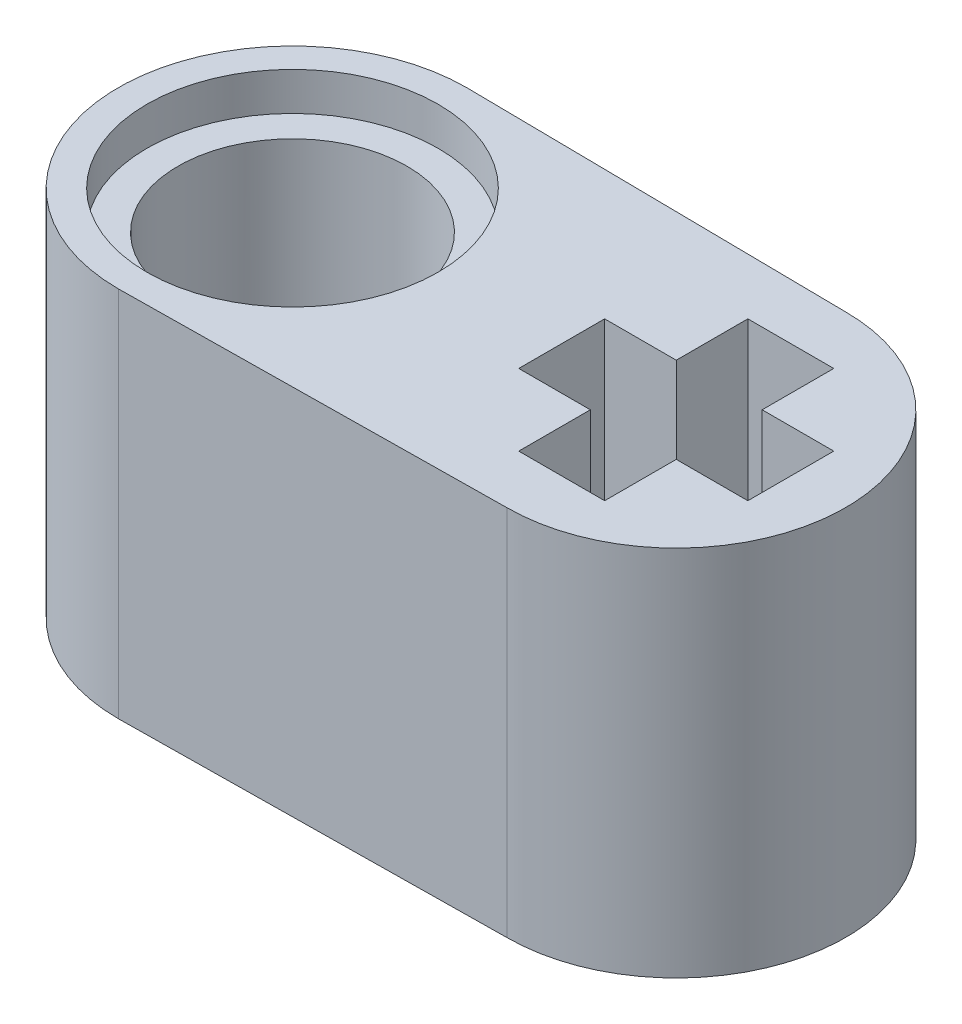
SolidWorks part; units mm, degrees
ref_plane "Front Plane" through (0, 0, 0) normal (0, 0, 1) x (1, 0, 0)
ref_plane "Top Plane" through (0, 0, 0) normal (0, 1, 0) x (1, 0, 0)
ref_plane "Right Plane" through (0, 0, 0) normal (1, 0, 0) x (0, 0, -1)
sketch "Sketch1" plane through (0, 0, 0) normal (0, 1, 0) x (1, 0, 0)
  line L0 (-1.67, 0) -> (3.97, 0) construction
  line L1 (-55, 0) -> (55, 0) construction
  line L2 (-4.07, 3.65) -> (3.97, 3.55)
  line L3 (-4.07, -3.65) -> (3.97, -3.55)
  line L6 (3.07, 2.4) -> (3.07, 0.9)
  line L7 (3.07, 2.4) -> (4.87, 2.4)
  line L8 (3.07, -2.4) -> (4.87, -2.4)
  line L9 (4.87, 2.4) -> (4.87, 0.9)
  line L10 (3.07, 2.4) -> (4.87, -2.4) construction
  line L11 (3.07, -2.4) -> (4.87, 2.4) construction
  line L12 (6.37, -0.9) -> (4.87, -0.9)
  line L13 (6.37, -0.9) -> (6.37, 0.9)
  line L14 (1.57, -0.9) -> (1.57, 0.9)
  line L15 (6.37, 0.9) -> (4.87, 0.9)
  line L16 (6.37, -0.9) -> (1.57, 0.9) construction
  line L17 (1.57, -0.9) -> (6.37, 0.9) construction
  line L18 (3.07, 0.9) -> (1.57, 0.9)
  line L19 (3.07, -0.9) -> (1.57, -0.9)
  line L20 (3.07, -0.9) -> (3.07, -2.4)
  line L21 (4.87, -0.9) -> (4.87, -2.4)
  arc A0 (-4.07, 3.65) -> (-4.07, -3.65) centre (-4.07, 0) ccw
  arc A1 (3.97, -3.55) -> (3.97, 3.55) centre (3.97, 0) ccw
  circle A2 centre (-4.07, 0) radius 2.4
  point P5 (0, 0)
  point P17 (3.97, 0)
  point P18 (3.97, 0)
  dimension "D3" = 8.04
  dimension "D1" = 7.3
  dimension "D2" = 15.24
extrude "Boss-Extrude1" add sketch "Sketch1" along normal blind 7.8
sketch "Sketch2" plane through (0, 7.8, 0) normal (0, 1, 0) x (1, 0, 0)
  line L0 (-4.29, 0) -> (4.29, 0) construction
  circle A0 centre (-4.07, 0) radius 3.05
  circle A1 centre (-4.07, 0) radius 2.4 construction
  dimension "D1" = 0
extrude "Cut-Extrude1" cut sketch "Sketch2" against normal blind 0.8
sketch "Sketch3" plane through (0, 0, 0) normal (0, -1, 0) x (1, 0, 0)
  circle A0 centre (-4.07, 0) radius 3.05
extrude "Cut-Extrude2" cut sketch "Sketch3" against normal blind 0.8
